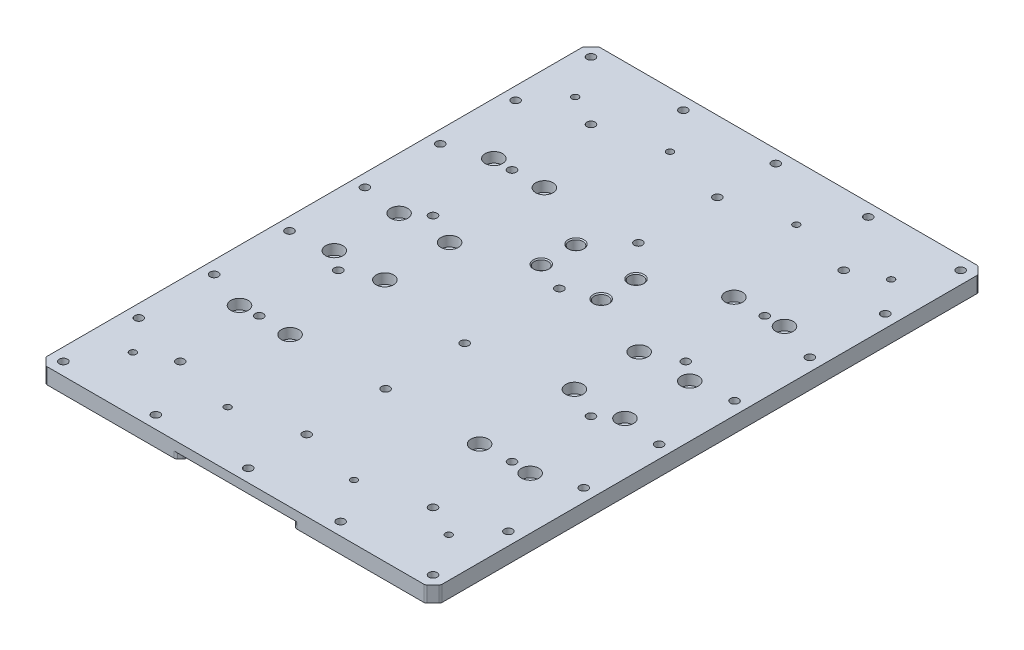
SolidWorks part; units mm, degrees
ref_plane "Front Plane" through (0, 0, 0) normal (0, 0, 1) x (1, 0, 0)
ref_plane "Top Plane" through (0, 0, 0) normal (0, 1, 0) x (1, 0, 0)
ref_plane "Right Plane" through (0, 0, 0) normal (1, 0, 0) x (0, 0, -1)
sketch "Sketch1" plane through (0, 0, 0) normal (0, 1, 0) x (1, 0, 0)
  line L0 (0, 0) -> (0, 350)
  line L1 (0, 350) -> (250, 350)
  line L2 (250, 350) -> (250, 0)
  line L3 (250, 0) -> (0, 0)
  line L4 (125, 350) -> (125, 0) construction
  dimension "D1" = 350
  dimension "D2" = 250
extrude "Boss-Extrude1" add sketch "Sketch1" along normal blind 10
sketch "Sketch2" plane through (0, 10, 0) normal (0, 1, 0) x (1, 0, 0)
  line L0 (125, 350) -> (125, 0) construction
  line L1 (250, 350) -> (0, 350) construction
  line L2 (0, 0) -> (250, 0) construction
  line L3 (106, 269.491) -> (106, 148.269) construction
  circle A0 centre (106, 234.5) radius 9.3248
  circle A1 centre (106, 212.5) radius 9.3248
  circle A2 centre (144, 212.5) radius 9.3248
  circle A3 centre (144, 234.5) radius 9.3248
  dimension "D1" = 19
  dimension "D2" = 22
  dimension "D3" = 212.5
hole_wizard "CBORE for M5 Hex Socket Head Cap Screw1" positions "3DSketch1" profile "Sketch3" counterbore size "M5" standard "ISO" end condition through all
sketch3d "3DSketch1"
  point P0 (106, 10, -234.5)
  point P3 (106, 10, -212.5)
  point P6 (144, 10, -212.5)
  point P9 (144, 10, -234.5)
sketch "Sketch3" plane through (106, 10, -234.5) normal (1, 0, 0) x (0, 0, 1)
  line L0 (0, 0) -> (0, 10)
  line L1 (0, 10) -> (2.75, 10)
  line L3 (2.75, 10) -> (2.75, 6.5)
  line L4 (4.4, 6.5) -> (2.75, 6.5)
  line L5 (4.4, 6.5) -> (4.4, 0.625)
  line L6 (4.4, 0.625) -> (5.025, 0)
  line L7 (5.025, 0) -> (0, 0)
  line L8 (-4.4, 0.625) -> (-5.025, 0) construction
  line L11 (0, -6.35) -> (0, 107.95) construction
  dimension "Thru Hole Dia." = 5.5
  dimension "Thru Hole Depth" = 10
  dimension "C'Bore Dia." = 8.8
  dimension "C'Bore Depth" = 6.5
  dimension "Near C'Sink Dia." = 10.05
  dimension "Near C'Sink Angle" = 90
chamfer "Chamfer1" distance 5 angle 45 4 edges at (0, 5, -350) (0, 5, 0) (250, 5, -350) (250, 5, 0)
sketch "Sketch4" plane through (0, 10, 0) normal (0, 1, 0) x (1, 0, 0)
  line L0 (0, 345) -> (0, 5) construction
  line L1 (245, 350) -> (5, 350) construction
  line L2 (0, 175) -> (250, 175) construction
  line L3 (250, 5) -> (250, 345) construction
  line L4 (125, 350) -> (125, 0) construction
  line L5 (5, 0) -> (245, 0) construction
  line L6 (8, 342) -> (8, -96.1302) construction
  line L7 (8, 342) -> (276.9014, 342) construction
  circle A0 centre (8, 342) radius 2.6
  circle A1 centre (66.5, 342) radius 2.6
  circle A2 centre (125, 342) radius 2.6
  circle A3 centre (8, 294.286) radius 2.6
  circle A4 centre (8, 246.572) radius 2.6
  circle A5 centre (8, 198.858) radius 2.6
  circle A6 centre (183.5, 342) radius 2.6
  circle A7 centre (242, 198.858) radius 2.6
  circle A8 centre (242, 246.572) radius 2.6
  circle A9 centre (242, 294.286) radius 2.6
  circle A10 centre (242, 342) radius 2.6
  circle A11 centre (242, 8) radius 2.6
  circle A12 centre (183.5, 8) radius 2.6
  circle A13 centre (125, 8) radius 2.6
  circle A14 centre (66.5, 8) radius 2.6
  circle A15 centre (8, 8) radius 2.6
  circle A16 centre (242, 55.714) radius 2.6
  circle A17 centre (242, 103.428) radius 2.6
  circle A18 centre (242, 151.142) radius 2.6
  circle A19 centre (8, 151.142) radius 2.6
  circle A20 centre (8, 103.428) radius 2.6
  circle A21 centre (8, 55.714) radius 2.6
  dimension "D1" = 5.2
  dimension "D2" = 8
  dimension "D3" = 8
  dimension "D4" = 58.5
  dimension "D5" = 47.714
  dimension "D6" = 47.714
  dimension "D7" = 47.714
extrude "Cut-Extrude1" cut sketch "Sketch4" against normal up to next
sketch "Sketch5" plane through (0, 10, 0) normal (0, 1, 0) x (1, 0, 0)
  line L0 (0, 175) -> (250, 175) construction
  line L1 (0, 345) -> (0, 5) construction
  line L2 (250, 5) -> (250, 345) construction
  line L3 (125, 350) -> (125, 0) construction
  line L4 (245, 350) -> (5, 350) construction
  line L5 (5, 0) -> (245, 0) construction
  line L6 (33, 255.5) -> (65, 255.5) construction
  line L7 (33, 195.5) -> (65, 195.5) construction
  line L9 (33, 255.5) -> (33, 160.1001) construction
  line L10 (65, 255.5) -> (65, 155.9115) construction
  circle A0 centre (33, 255.5) radius 2.5
  circle A1 centre (65, 255.5) radius 2.5
  circle A2 centre (33, 195.5) radius 2.5
  circle A3 centre (65, 195.5) radius 2.5
  circle A16 centre (65, 154.5) radius 2.5
  circle A17 centre (33, 154.5) radius 2.5
  circle A18 centre (65, 94.5) radius 2.5
  circle A19 centre (33, 94.5) radius 2.5
  circle A20 centre (185, 94.5) radius 2.5
  circle A21 centre (217, 94.5) radius 2.5
  circle A22 centre (185, 154.5) radius 2.5
  circle A23 centre (217, 154.5) radius 2.5
  circle A24 centre (185, 195.5) radius 2.5
  circle A25 centre (217, 195.5) radius 2.5
  circle A26 centre (185, 255.5) radius 2.5
  circle A27 centre (217, 255.5) radius 2.5
  dimension "D5" = 5
  dimension "D1" = 60
  dimension "D2" = 20.5
  dimension "D3" = 32
  dimension "D4" = 32
  dimension "D6" = 120
hole_wizard "CBORE for M6 Hex Socket Head Cap Screw1" positions "3DSketch2" profile "Sketch6" counterbore size "M6" standard "ISO" end condition through all
sketch3d "3DSketch2"
  point P0 (33, 10, -255.5)
  point P3 (65, 10, -255.5)
  point P12 (185, 10, -255.5)
  point P15 (217, 10, -195.5)
  point P18 (185, 10, -195.5)
  point P21 (217, 10, -154.5)
  point P24 (185, 10, -154.5)
  point P36 (217, 10, -94.5)
  point P42 (185, 10, -94.5)
  point P50 (33, 10, -94.5)
  point P53 (65, 10, -94.5)
  point P56 (33, 10, -154.5)
  point P59 (65, 10, -154.5)
  point P62 (33, 10, -195.5)
  point P65 (65, 10, -195.5)
  point P68 (217, 10, -255.5)
sketch "Sketch6" plane through (33, 10, -255.5) normal (1, 0, 0) x (0, 0, 1)
  line L0 (0, 0) -> (0, 10)
  line L1 (0, 10) -> (3.1, 10)
  line L3 (3.1, 10) -> (3.1, 6.4)
  line L4 (3.1, 6.4) -> (5.5, 6.4)
  line L5 (5.5, 6.4) -> (5.5, 0)
  line L7 (5.5, 0) -> (0, 0)
  line L11 (0, -6.35) -> (0, 107.95) construction
  dimension "Thru Hole Dia." = 6.2
  dimension "Thru Hole Depth" = 10
  dimension "C'Bore Dia." = 11
  dimension "C'Bore Depth" = 6.4
sketch "Sketch7" plane through (0, 0, 0) normal (0, -1, 0) x (1, 0, 0)
  line L0 (125, 0) -> (125, -350) construction
  line L1 (5, 0) -> (245, 0) construction
  line L2 (245, -350) -> (5, -350) construction
  line L3 (160, 0) -> (90, 0)
  line L4 (90, 0) -> (90, -160)
  line L5 (90, -160) -> (160, -160)
  line L6 (160, -160) -> (160, 0)
  dimension "D1" = 70
  dimension "D2" = 160
extrude "Cut-Extrude2" cut sketch "Sketch7" against normal blind 4
chamfer "Chamfer2" distance 3 angle 45 2 edges at (160, 2, 0) (90, 2, 0)
fillet "Fillet1" radius 2 12 edges at (250, 5, -345) (245, 5, -350) (0, 5, -345) (5, 5, -350) (5, 5, 0) (0, 5, -5) (87, 2, 0) (90, 2, -3) (160, 2, -3) (163, 2, 0) (245, 5, 0) (250, 5, -5)
sketch "Sketch8" plane through (0, 10, 0) normal (0, 1, 0) x (1, 0, 0)
  line L0 (125, 350) -> (125, 0) construction
  line L1 (244.1716, 350) -> (5.8284, 350) construction
  line L2 (5.8284, 0) -> (244.1716, 0) construction
  line L3 (25, 35) -> (85, 35) construction
  line L4 (0, 344.1716) -> (0, 5.8284) construction
  line L5 (0, 175) -> (250, 175) construction
  line L6 (250, 5.8284) -> (250, 344.1716) construction
  point P14 (85, 315)
  point P15 (25, 315)
  point P16 (165, 315)
  point P17 (225, 315)
  point P18 (165, 35)
  point P19 (225, 35)
  dimension "D1" = 25
  dimension "D2" = 60
  dimension "D3" = 35
hole_wizard "M5 Tapped Hole1" positions "3DSketch3" profile "Sketch9" tap size "M5" standard "GB"
sketch3d "3DSketch3"
  point P0 (25, 10, -35)
  point P3 (85, 10, -35)
  point P6 (165, 10, -35)
  point P9 (225, 10, -35)
  point P12 (25, 10, -315)
  point P15 (85, 10, -315)
  point P18 (165, 10, -315)
  point P21 (225, 10, -315)
sketch "Sketch9" plane through (25, 10, -35) normal (1, 0, 0) x (0, 0, 1)
  line L0 (0, 0) -> (0, 15.2618)
  line L1 (0, 15.2618) -> (2.1, 14)
  line L2 (2.1, 14) -> (2.1, 0)
  line L5 (2.1, 0) -> (0, 0)
  line L10 (0, 15.2618) -> (-2.1, 14) construction
  line L11 (0, -6.35) -> (0, 107.95) construction
  dimension "Tap Drill Dia." = 4.2
  dimension "Tap Drill Depth" = 14
  dimension "Drill Angle" = 118
cosmetic thread "Hole Thread1" parameters "D1"=10, "D2"=5
cosmetic thread "Hole Thread2" parameters "D1"=10, "D2"=5
cosmetic thread "Hole Thread3" parameters "D1"=10, "D2"=5
cosmetic thread "Hole Thread4" parameters "D1"=10, "D2"=5
cosmetic thread "Hole Thread5" parameters "D1"=10, "D2"=5
cosmetic thread "Hole Thread6" parameters "D1"=10, "D2"=5
cosmetic thread "Hole Thread7" parameters "D1"=10, "D2"=5
cosmetic thread "Hole Thread8" parameters "D1"=10, "D2"=5
sketch "Sketch10" plane through (0, 10, 0) normal (0, 1, 0) x (1, 0, 0)
  line L0 (125, 350) -> (125, 0) construction
  line L1 (244.1716, 350) -> (5.8284, 350) construction
  line L2 (5.8284, 0) -> (244.1716, 0) construction
  line L3 (45, 350) -> (45, 0) construction
  line L5 (45, 45) -> (205, 45) construction
  line L6 (45, 95) -> (205, 95) construction
  line L7 (45, 145) -> (205, 145) construction
  line L8 (45, 205) -> (205, 205) construction
  line L9 (45, 255) -> (205, 255) construction
  line L10 (45, 305) -> (205, 305) construction
  circle A0 centre (45, 305) radius 5
  circle A1 centre (45, 255) radius 5
  circle A2 centre (45, 205) radius 5
  circle A3 centre (45, 145) radius 5
  circle A4 centre (45, 95) radius 5
  circle A5 centre (45, 45) radius 5
  circle A6 centre (205, 45) radius 5
  circle A7 centre (205, 95) radius 5
  circle A8 centre (205, 145) radius 5
  circle A9 centre (205, 205) radius 5
  circle A10 centre (205, 255) radius 5
  circle A11 centre (205, 305) radius 5
  circle A12 centre (125, 305) radius 5
  circle A13 centre (125, 255) radius 5
  circle A14 centre (125, 205) radius 5
  circle A15 centre (125, 145) radius 5
  circle A16 centre (125, 95) radius 5
  circle A17 centre (125, 45) radius 5
  dimension "D2" = 10
  dimension "D8" = 50
  dimension "D9" = 10
  dimension "D1" = 80
  dimension "D3" = 45
  dimension "D4" = 50
  dimension "D5" = 50
  dimension "D6" = 60
  dimension "D7" = 50
hole_wizard "M6 Tapped Hole1" positions "3DSketch4" profile "Sketch11" tap size "M6" standard "GB"
sketch3d "3DSketch4"
  point P0 (45, 10, -45)
  point P3 (205, 10, -45)
  point P6 (205, 10, -95)
  point P9 (45, 10, -95)
  point P12 (45, 10, -145)
  point P15 (205, 10, -145)
  point P18 (205, 10, -205)
  point P21 (45, 10, -205)
  point P24 (45, 10, -255)
  point P27 (205, 10, -255)
  point P30 (205, 10, -305)
  point P33 (45, 10, -305)
  point P37 (125, 10, -45)
  point P40 (125, 10, -95)
  point P43 (125, 10, -145)
  point P46 (125, 10, -205)
  point P49 (125, 10, -255)
  point P52 (125, 10, -305)
sketch "Sketch11" plane through (45, 10, -45) normal (1, 0, 0) x (0, 0, 1)
  line L0 (0, 0) -> (0, 18.5622)
  line L1 (0, 18.5622) -> (2.6, 17)
  line L2 (2.6, 17) -> (2.6, 0)
  line L5 (2.6, 0) -> (0, 0)
  line L10 (0, 18.5622) -> (-2.6, 17) construction
  line L11 (0, -6.35) -> (0, 107.95) construction
  dimension "Tap Drill Dia." = 5.2
  dimension "Tap Drill Depth" = 17
  dimension "Drill Angle" = 118
cosmetic thread "Hole Thread9" parameters "D1"=10, "D2"=6
cosmetic thread "Hole Thread10" parameters "D1"=10, "D2"=6
cosmetic thread "Hole Thread11" parameters "D1"=10, "D2"=6
cosmetic thread "Hole Thread12" parameters "D1"=10, "D2"=6
cosmetic thread "Hole Thread13" parameters "D1"=10, "D2"=6
cosmetic thread "Hole Thread14" parameters "D1"=10, "D2"=6
cosmetic thread "Hole Thread15" parameters "D1"=10, "D2"=6
cosmetic thread "Hole Thread16" parameters "D1"=10, "D2"=6
cosmetic thread "Hole Thread17" parameters "D1"=10, "D2"=6
cosmetic thread "Hole Thread18" parameters "D1"=10, "D2"=6
cosmetic thread "Hole Thread19" parameters "D1"=10, "D2"=6
cosmetic thread "Hole Thread20" parameters "D1"=10, "D2"=6
cosmetic thread "Hole Thread21" parameters "D1"=10, "D2"=6
cosmetic thread "Hole Thread22" parameters "D1"=10, "D2"=6
cosmetic thread "Hole Thread23" parameters "D1"=10, "D2"=6
cosmetic thread "Hole Thread24" parameters "D1"=6, "D2"=6
cosmetic thread "Hole Thread25" parameters "D1"=6, "D2"=6
cosmetic thread "Hole Thread26" parameters "D1"=6, "D2"=6
